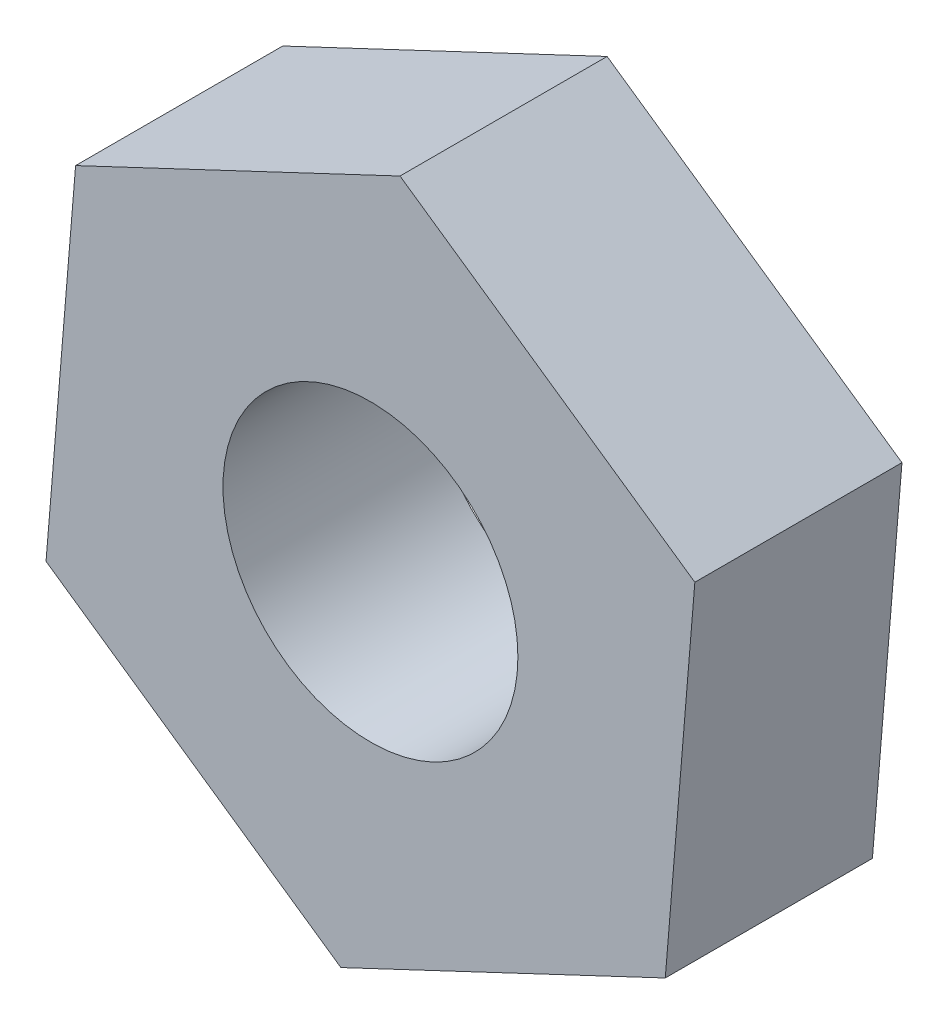
SolidWorks part; units mm, degrees
ref_plane "Front Plane" through (0, 0, 0) normal (0, 0, 1) x (1, 0, 0)
ref_plane "Top Plane" through (0, 0, 0) normal (0, 1, 0) x (1, 0, 0)
ref_plane "Right Plane" through (0, 0, 0) normal (1, 0, 0) x (0, 0, -1)
sketch "Sketch1" plane through (0, 0, 0) normal (0, 0, 1) x (1, 0, 0)
  line L1 (2.2599, -1.5664) -> (2.4864, 1.1739)
  line L2 (2.4864, 1.1739) -> (0.2266, 2.7403)
  line L3 (0.2266, 2.7403) -> (-2.2599, 1.5664)
  line L4 (-2.2599, 1.5664) -> (-2.4864, -1.1739)
  line L5 (-2.4864, -1.1739) -> (-0.2266, -2.7403)
  line L6 (-0.2266, -2.7403) -> (2.2599, -1.5664)
  circle A0 centre (0, 0) radius 2.3812 construction
  dimension "D1" = 4.7625
extrude "Boss-Extrude1" add sketch "Sketch1" along normal blind 1.5875
hole_wizard "#4-40 Tapped Hole1" positions "Sketch3" profile "Sketch2" tap size "#4-40" standard "ANSI Inch" end condition through all
sketch "Sketch3" plane through (0, 0, 1.5875) normal (0, 0, 1) x (1, 0, 0)
  point P0 (0, 0)
  point P1 (0, 0)
  point P2 (0, 0)
  point P4 (0, 0)
sketch "Sketch2" plane through (0, 0, 1.5875) normal (1, 0, 0) x (0, -1, 0)
  line L0 (0, 0) -> (0, 1.5875)
  line L1 (0, 1.5875) -> (1.1303, 1.5875)
  line L2 (1.1303, 1.5875) -> (1.1303, 0)
  line L5 (1.1303, 0) -> (0, 0)
  line L11 (0, -6.35) -> (0, 107.95) construction
  dimension "Thru Tap Drill Dia." = 2.2606
  dimension "Thru Tap Drill Depth" = 1.5875
cosmetic thread "Hole Thread1"
